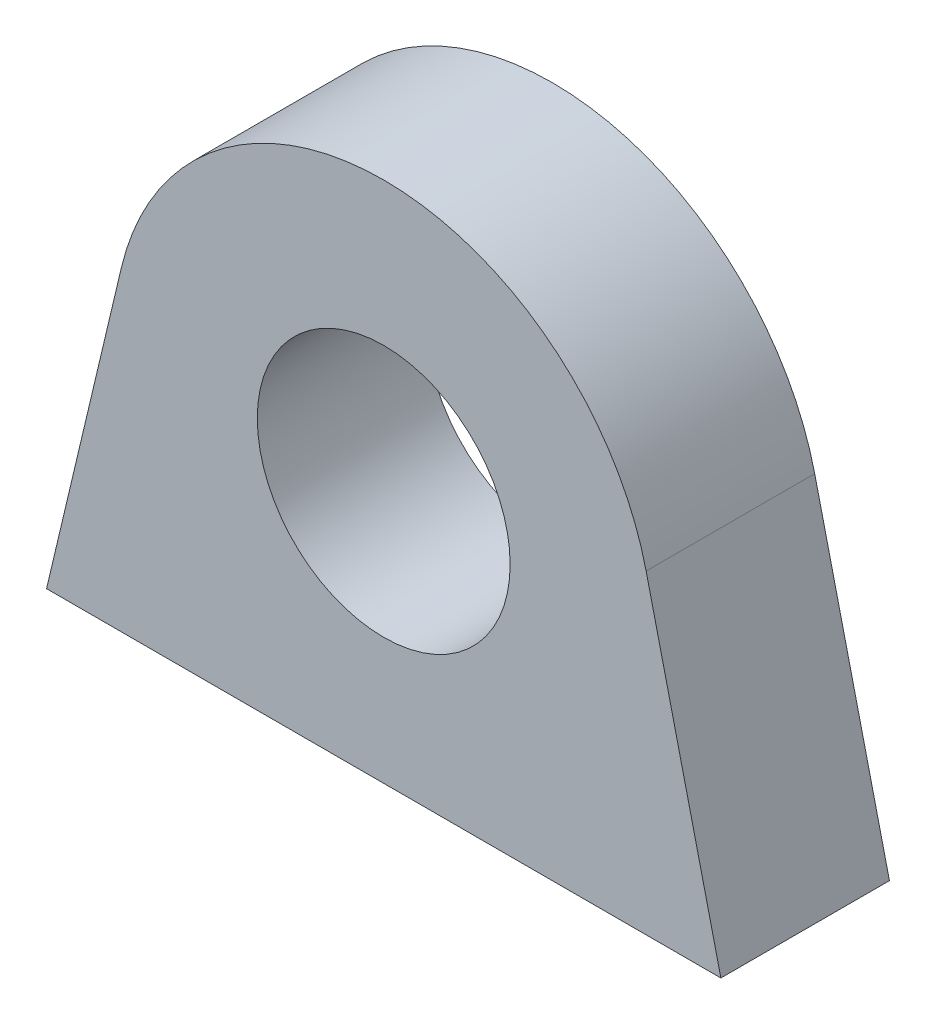
SolidWorks part; units mm, degrees
ref_plane "Front Plane" through (0, 0, 0) normal (0, 0, 1) x (1, 0, 0)
ref_plane "Top Plane" through (0, 0, 0) normal (0, 1, 0) x (1, 0, 0)
ref_plane "Right Plane" through (0, 0, 0) normal (1, 0, 0) x (0, 0, -1)
sketch "Sketch1" plane through (0, 0, 0) normal (0, 0, 1) x (1, 0, 0)
  line L0 (-20, 0) -> (20, 0)
  line L1 (20, 0) -> (15.5666, 18.6921)
  line L3 (-15.5666, 18.6921) -> (-20, 0)
  line L4 (0, 7.1554) -> (0, -10.7918) construction
  arc A0 (-15.5666, 18.6921) -> (15.5666, 18.6921) centre (0, 15) cw
  circle A1 centre (0, 15) radius 7.5
  point P3 (0, 0)
  point P8 (0, 0)
  point P9 (0, 0)
  dimension "D2" = 15
  dimension "D1" = 40
  dimension "D3" = 15
extrude "Boss-Extrude1" add sketch "Sketch1" along normal blind 10
